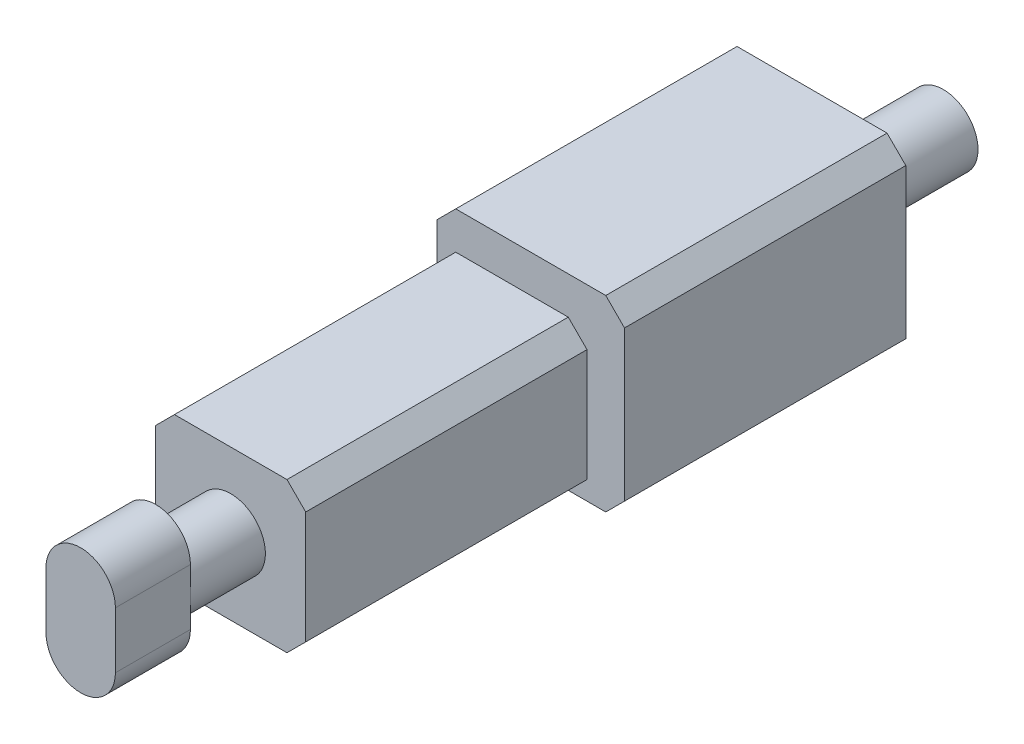
SolidWorks part; units mm, degrees
material "ABS"
ref_plane "Front Plane" through (0, 0, 0) normal (0, 0, 1) x (1, 0, 0)
ref_plane "Top Plane" through (0, 0, 0) normal (0, 1, 0) x (1, 0, 0)
ref_plane "Right Plane" through (0, 0, 0) normal (1, 0, 0) x (0, 0, -1)
sketch "Sketch1" plane through (0, 0, 0) normal (0, 1, 0) x (1, 0, 0)
  line L1 (-2, -7.5) -> (2, -7.5)
  line L2 (-2, -7.5) -> (-2, 7.5)
  line L3 (-2, 7.5) -> (2, 7.5)
  line L4 (2, -7.5) -> (2, 7.5)
  line L5 (-2, -7.5) -> (2, 7.5) construction
  line L6 (-2, 7.5) -> (2, -7.5) construction
  point P0 (0, 0)
  dimension "D1" = 15
  dimension "D2" = 4
extrude "Boss-Extrude1" add sketch "Sketch1" along normal blind 4
sketch "Sketch2" plane through (0, 0, 7.5) normal (0, 0, 1) x (1, 0, 0)
  line L3 (0, 0) -> (0, 4) construction
  line L4 (-2, 4) -> (2, 4) construction
  line L5 (-2, 2) -> (2, 2) construction
  line L6 (-2, 4) -> (-2, 0) construction
  line L7 (2, 4) -> (2, 0) construction
  circle A2 centre (0, 2) radius 0.925
  dimension "D1" = 1.85
extrude "Boss-Extrude2" add sketch "Sketch2" along normal blind 2
sketch "Sketch3" plane through (0, 0, 9.5) normal (0, 0, 1) x (1, 0, 0)
  line L0 (0, 1.25) -> (0, 2.75) construction
  line L3 (-0.925, 1.25) -> (-0.925, 2.75)
  line L4 (0.925, 1.25) -> (0.925, 2.75)
  arc A2 (-0.925, 1.25) -> (0.925, 1.25) centre (0, 1.25) ccw
  arc A3 (0.925, 2.75) -> (-0.925, 2.75) centre (0, 2.75) ccw
  point P2 (0, 2)
  dimension "D1" = 0.75
  dimension "D2" = 1.85
extrude "Boss-Extrude3" add sketch "Sketch3" along normal blind 2
sketch "Sketch6" plane through (0, 0, 0) normal (0, 0, 1) x (1, 0, 0)
  line L1 (-2, 0) -> (3, 0)
  line L2 (-2, 0) -> (-2, 5)
  line L3 (-2, 5) -> (3, 5)
  line L4 (3, 0) -> (3, 5)
  dimension "D1" = 5
  dimension "D2" = 5
extrude "Boss-Extrude5" add sketch "Sketch6" against normal blind 7.5
sketch "Sketch7" plane through (0, 0, 7.5) normal (0, 0, 1) x (1, 0, 0)
  line L0 (-2, 2) -> (2, 2) construction
  line L1 (-2, 4) -> (-2, 0) construction
  line L2 (2, 4) -> (2, 0) construction
  line L3 (0, 4) -> (0, 0) construction
  line L4 (-2, 4) -> (2, 4) construction
  circle A0 centre (1, 2.8329) radius 0.925
  point P13 (1.304, 1.8329)
  point P14 (0, 2)
  dimension "D3" = 1.85
  dimension "D1" = 1
  dimension "D2" = 1
extrude "Boss-Extrude6" add sketch "Sketch7" against normal blind 18
chamfer "Chamfer1" distance 0.5 angle 45 7 edges at (-2, 0, 0) (-2, 4, 3.75) (2, 0, 3.75) (2, 4, 3.75) (3, 0, -3.75) (3, 5, -3.75) (-2, 5, -3.75)
